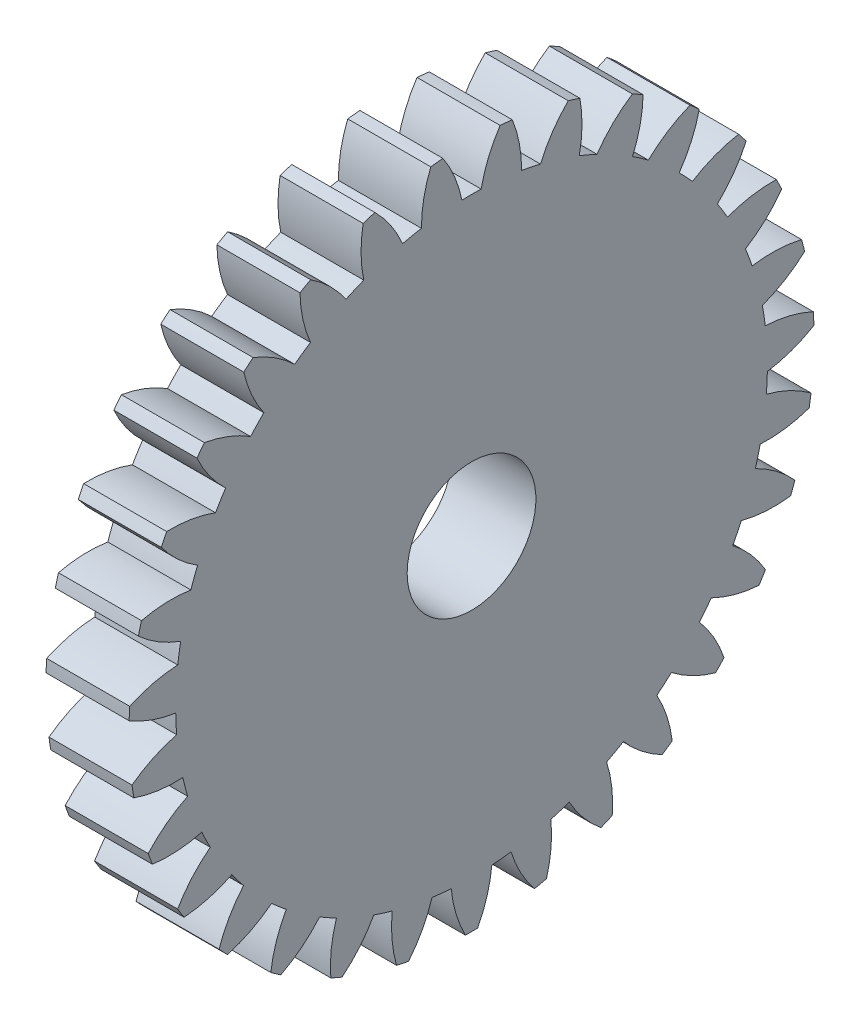
SolidWorks part; units mm, degrees
ref_plane "Plane1" through (0, 0, 0) normal (0, 0, 1) x (1, 0, 0)
ref_plane "Plane2" through (0, 0, 0) normal (0, 1, 0) x (1, 0, 0)
ref_plane "Plane3" through (0, 0, 0) normal (1, 0, 0) x (0, 0, -1)
sketch "HoldingSke" plane through (0, 0, 0) normal (0, 1, 0) x (1, 0, 0)
  line L0 (0, 0) -> (0.8572, -0.515)
  line L1 (-15, 0) -> (100, 0) construction
  line L2 (0, 0) -> (-2.1039, 2.3779)
  line L3 (0, 0) -> (-11.863, 4.5341)
  line L4 (0, 0) -> (7.4025, 4.4479)
  line L5 (0, 0) -> (-46.8476, -17.4728)
  line L6 (0, 0) -> (-3.3159, -2.2372)
  line L7 (-2.1039, 2.3779) -> (8.6586, 51.2059)
  line L8 (-76.2, 54.61) -> (-75.7, 54.61)
  line L9 (-71.009, 38.7566) -> (-53.1078, 45.2721)
  line L10 (-76.2, 71.12) -> (104.1128, 71.12)
  line L11 (0, 0) -> (-4, 0)
  line L12 (-76.2, 101.6) -> (-76.162, 101.6)
  line L13 (24.9733, 27.94) -> (52.9518, 28.4284)
  line L14 (24.9733, 27.94) -> (24.9743, 27.94)
  line L15 (24.9733, 27.94) -> (100.4006, 29.5858)
  line L16 (-63.627, -1) -> (-12.827, -1)
  circle A0 centre (0, 0) radius 1.5
  circle A1 centre (0, 0) radius 14.249
  circle A2 centre (0, 0) radius 37.5
  circle A3 centre (0, 0) radius 1.5
  dimension "MHD" = 28.498
  dimension "Hub_dia" = 75
  dimension "Bore" = 3
  dimension "MBD" = 3
  dimension "Num_teeth" = 31
  dimension "Pitch" = 1
  dimension "Overall_len" = 50
  dimension "Show_teeth" = 31
  dimension "Thickness" = 4
  dimension "OAL" = 50.0001
  dimension "T_dim" = 0.5
  dimension "Ap" = 20
  dimension "H" = 19.05
  dimension "Pitch_radius" = 180.3128
  dimension "Width" = 4
  dimension "Backlash" = 0.038
  dimension "Addendum_fac" = 1
  dimension "Dedendum_fac" = 1.25
  dimension "Clearance_fac" = 0.25
  dimension "Dedendum_add" = 0.001
  dimension "Module" = 1
sketch "BasProSke" plane through (0, 0, 0) normal (0, 1, 0) x (1, 0, 0)
  line L0 (-10, 0) -> (60, 0) construction
  line L1 (0, 0) -> (0, 16.5)
  line L2 (0, 0) -> (4, 0)
  line L3 (4, 0) -> (4, 16.5)
  line L4 (4, 16.5) -> (0, 16.5)
  dimension "Thickness" = 4
  dimension "Diameter" = 33
revolve "Base-Revolve" add sketch "BasProSke" angle 360 about L0
sketch "TooCutSke" plane through (0, 0, 0) normal (1, 0, 0) x (0, 0, -1)
  line L1 (0, 0) -> (0, 107) construction
  line L2 (0, 0) -> (-0.8515, 15.4766) construction
  line L3 (0, 0) -> (-3.1328, 30.8078) construction
  line L4 (-0.8515, 15.4766) -> (-1.5664, 15.4039) construction
  arc A0 (0.4642, 14.2414) -> (-0.4642, 14.2414) centre (0, 0) ccw
  arc A1 (1.3919, 16.4667) -> (-1.3919, 16.4667) centre (0, 0) ccw
  circle A2 centre (0, 0) radius 15.5 construction
  circle A3 centre (0, 0) radius 14.5652 construction
  arc A4 (-0.4642, 14.2414) -> (-1.3919, 16.4667) centre (-6.5414, 13.0137) ccw
  arc A5 (1.3919, 16.4667) -> (0.4642, 14.2414) centre (6.5414, 13.0137) ccw
  dimension "Root_dia" = 28.498
  dimension "Overcut_dia" = 33.0508
  dimension "Pitch_dia" = 31
  dimension "Base_dia" = 29.1305
  dimension "Flank_rad" = 6.2
  dimension "Half_ang" = 5.806
  dimension "Half_CT" = 0.7186
extrude "ToothCut" cut sketch "TooCutSke" along normal through all
fillet "Breaks" [suppressed] radius 0.02
fillet "RootFillets" [suppressed] radius 0.251
pattern_circular "TeethCuts" count 31 every 11.613 about axis through (-10, 0, 0) along (1, 0, 0) of "ToothCut", "RootFillets", "Breaks"
sketch "HubNeaOneSke" plane through (0, 0, 0) normal (-1, 0, 0) x (0, 0, 1)
  circle A0 centre (0, 0) radius 14.249
  dimension "Diameter" = 28.498
extrude "HubNearOne" [suppressed] add sketch "HubNeaOneSke" along normal blind 46.0001
sketch "HubNeaBotSke" plane through (0, 0, 0) normal (-1, 0, 0) x (0, 0, 1)
  circle A0 centre (0, 0) radius 14.249
  dimension "Diameter" = 28.498
extrude "HubNearBoth" [suppressed] add sketch "HubNeaBotSke" along normal blind 23
ref_plane "FarPln" through (4, 0, 0) normal (1, 0, 0) x (0, 0, -1)
sketch "HubFarSke" plane through (4, 0, 0) normal (1, 0, 0) x (0, 0, -1)
  circle A0 centre (0, 0) radius 14.249
  dimension "Diameter" = 28.498
extrude "HubFar" [suppressed] add sketch "HubFarSke" along normal blind 23
sketch "BorSke" plane through (0, 0, 0) normal (1, 0, 0) x (0, 0, -1)
  circle A0 centre (0, 0) radius 3.1
  dimension "Diameter" = 6.2
extrude "Bore" cut sketch "BorSke" along normal mid plane 100.0001
sketch "KeySke" plane through (0, 0, 0) normal (1, 0, 0) x (0, 0, -1)
  line L0 (-0.6, 0) -> (-0.6, 2)
  line L1 (-0.6, 2) -> (0.6, 2)
  line L2 (0.6, 2) -> (0.6, 0)
  line L3 (0, 0) -> (0, 34) construction
  line L4 (-0.6, 0) -> (0.6, 0)
  dimension "Offset" = 2
  dimension "Width" = 1.2
extrude "Keyway" [suppressed] cut sketch "KeySke" along normal mid plane 100.0001
pattern_circular "Keyway2" [suppressed] count 2 every 90 about axis through (-10, 0, 0) along (1, 0, 0)
equation "' \"Module@HoldingSke\" = 6.35"
equation "' \"Num_teeth@HoldingSke\" = 12"
equation "' \"Ap@HoldingSke\" =  20"
equation "' \"Ap@HoldingSke\" = 20"
equation "' \"Width@HoldingSke\" = 0.5 * 25.4"
equation "' \"Hub_dia@HoldingSke\"= 1 * 25.4"
equation "' \"Hub_dia@HoldingSke\" = 1 * 25.4"
equation "' \"Overall_len@HoldingSke\" = 1.0 * 25.4"
equation "' \"Bore@HoldingSke\" = 0.75 * 25.4"
equation "' \"T_dim@HoldingSke\" = 0.1 * 25.4"
equation "' \"Width@KeySke\" = 0.25 * 25.4"
equation "' \"Show_teeth@HoldingSke\" = 13"
equation "' \"Backlash@HoldingSke\" = 0.009 * 25.4"
equation "' \"Addendum_fac@HoldingSke\" = 1.0"
equation "' \"Dedendum_fac@HoldingSke\" = 1.25"
equation "' \"Dedendum_add@HoldingSke\" = 0.00005 * 25.4"
equation "' \"Clearance_fac@HoldingSke\" = 0.25"
equation "\"Pitch@HoldingSke\" = 1 / \"Module@HoldingSke\""
equation "\"Overcut_dia@TooCutSke\" = (\"Num_teeth@HoldingSke\" + 2 * \"Addendum_fac@HoldingSke\") / \"Pitch@HoldingSke\" + 0.002 * 25.4"
equation "\"Pitch_dia@TooCutSke\" = \"Num_teeth@HoldingSke\" / \"Pitch@HoldingSke\""
equation "\"Base_dia@TooCutSke\" = \"Num_teeth@HoldingSke\" / \"Pitch@HoldingSke\" * cos((\"Ap@HoldingSke\"  * 3.14159265 / 180))"
equation "\"Root_dia@TooCutSke\" = (\"Num_teeth@HoldingSke\" + 2) / \"Pitch@HoldingSke\" - 2 * (\"Addendum_fac@HoldingSke\" + \"Dedendum_fac@HoldingSke\") / \"Pitch@HoldingSke\" - \"Dedendum_add@HoldingSke\" * 2"
equation "\"Half_ang@TooCutSke\" = 180 / \"Num_teeth@HoldingSke\""
equation "\"Half_CT@TooCutSke\" = \"Num_teeth@HoldingSke\" / \"Pitch@HoldingSke\" * sin((3.14159265 / 2 / \"Num_teeth@HoldingSke\")) / 2 - 7 * \"Backlash@HoldingSke\" / 4"
equation "\"Flank_rad@TooCutSke\" = \"Num_teeth@HoldingSke\" / \"Pitch@HoldingSke\" / 5"
equation "\"Radius@RootFillets\" = \"Clearance_fac@HoldingSke\" / \"Pitch@HoldingSke\" + \"Dedendum_add@HoldingSke\""
equation "\"Break_rad@Breaks\" = 0.02 / \"Pitch@HoldingSke\""
equation "\"Thickness@HoldingSke\" = \"Width@HoldingSke\""
equation "\"OAL@HoldingSke\" = \"Thickness@HoldingSke\""
equation "\"MHD@HoldingSke\" = (\"Num_teeth@HoldingSke\" + 2) / \"Pitch@HoldingSke\" - 2 * (\"Addendum_fac@HoldingSke\" + \"Dedendum_fac@HoldingSke\")  / \"Pitch@HoldingSke\" - \"Dedendum_add@HoldingSke\" * 2"
equation "\"MBD@HoldingSke\" = (\"Num_teeth@HoldingSke\" + 2) / \"Pitch@HoldingSke\" - 2 * (\"Addendum_fac@HoldingSke\" + \"Dedendum_fac@HoldingSke\")  / \"Pitch@HoldingSke\" - \"Dedendum_add@HoldingSke\" * 2 - 0.002 * 25.4"
equation "\"MHD@HoldingSke\" = ((sgn( \"MHD@HoldingSke\" - \"Hub_dia@HoldingSke\" )-1)*( \"MHD@HoldingSke\" - \"Hub_dia@HoldingSke\" ))/-2+ \"Hub_dia@HoldingSke\""
equation "\"MBD@HoldingSke\" = ((sgn( \"MBD@HoldingSke\" - \"Bore@HoldingSke\" )-1)*( \"MBD@HoldingSke\" - \"Bore@HoldingSke\" ))/-2+ \"Bore@HoldingSke\""
equation "\"OAL@HoldingSke\" = ((sgn( \"OAL@HoldingSke\" - \"Overall_len@HoldingSke\" )+1)*( \"OAL@HoldingSke\" - \"Overall_len@HoldingSke\" ))/2 + \"Overall_len@HoldingSke\" + 0.000002 * 25.4"
equation "\"Num_teeth@TeethCuts\" = int( \"Show_teeth@HoldingSke\" ) + 1"
equation "\"Num_teeth@TeethCuts\" = ((sgn( \"Num_teeth@TeethCuts\" - \"Num_teeth@HoldingSke\" )-1)*( \"Num_teeth@TeethCuts\" - \"Num_teeth@HoldingSke\" ))/-2+ \"Num_teeth@HoldingSke\""
equation "\"Num_teeth@TeethCuts\" = ((sgn( \"Num_teeth@TeethCuts\" - 2.0)+1)*( \"Num_teeth@TeethCuts\" - 2.0))/2 +2.0"
equation "\"Angle@TeethCuts\" = 360.0 / \"Num_teeth@HoldingSke\""
equation "\"Diameter@BasProSke\" = (\"Num_teeth@HoldingSke\" + 2 * \"Addendum_fac@HoldingSke\") / \"Pitch@HoldingSke\""
equation "\"Thickness@BasProSke\"  = \"Thickness@HoldingSke\""
equation "' \"Fillet_rad@BasProSke\" =  \"Thickness@HoldingSke\" * 0.05"
equation "' \"Fillet_rad@BasProSke\" = \"Thickness@HoldingSke\" * 0.05"
equation "\"MHD@HoldingSke\" = ((sgn( \"MHD@HoldingSke\" - \"Root_dia@TooCutSke\" )-1)*( \"MHD@HoldingSke\" - \"Root_dia@TooCutSke\" ))/-2+ \"Root_dia@TooCutSke\""
equation "\"Diameter@HubNeaOneSke\" = \"MHD@HoldingSke\""
equation "\"Length@HubNearOne\" = \"OAL@HoldingSke\" - \"Thickness@BasProSke\""
equation "\"Diameter@HubNeaBotSke\" = \"MHD@HoldingSke\""
equation "\"Length@HubNearBoth\" = ( \"OAL@HoldingSke\" - \"Thickness@BasProSke\" ) / 2.0"
equation "\"Thickness@FarPln\" = \"Thickness@BasProSke\""
equation "\"Diameter@HubFarSke\" = \"MHD@HoldingSke\""
equation "\"Length@HubFar\" = ( \"OAL@HoldingSke\" - \"Thickness@BasProSke\" ) / 2.0"
equation "\"D1@Bore\" = \"OAL@HoldingSke\" * 2.0"
equation "\"D1@Keyway\" = \"OAL@HoldingSke\" * 2.0"
equation "\"Offset@KeySke\" = \"T_dim@HoldingSke\" + \"MBD@HoldingSke\" / 2.0"
